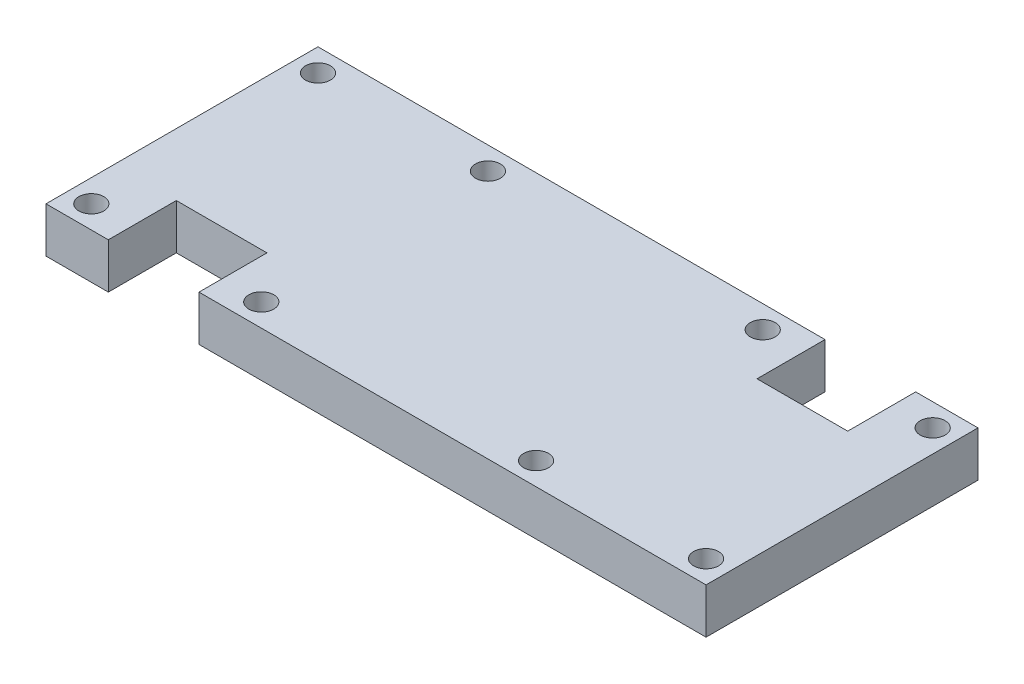
SolidWorks part; units mm, degrees
material "Alliage 1060"
ref_plane "Plan de face" through (0, 0, 0) normal (0, 0, 1) x (1, 0, 0)
ref_plane "Plan de dessus" through (0, 0, 0) normal (0, 1, 0) x (1, 0, 0)
ref_plane "Plan de droite" through (0, 0, 0) normal (1, 0, 0) x (0, 0, -1)
sketch "Esquisse1" plane through (0, 0, 0) normal (0, 1, 0) x (1, 0, 0)
  line L0 (0, 0) -> (38, 0)
  line L1 (38, 0) -> (38, 48) construction
  line L2 (38, 48) -> (0, 48)
  line L3 (0, 48) -> (0, 0)
  line L4 (58.25, 48) -> (58.25, 0) construction
  line L5 (116.5, 48) -> (116.5, 0)
  line L6 (78.5, 48) -> (116.5, 48)
  line L7 (78.5, 0) -> (78.5, 48) construction
  line L8 (116.5, 0) -> (78.5, 0)
  line L9 (38, 48) -> (78.5, 48)
  line L10 (38, 0) -> (78.5, 0)
  dimension "D1" = 38
  dimension "D2" = 48
  dimension "D3" = 20.25
extrude "Boss.-Extru.1" add sketch "Esquisse1" along normal blind 8
sketch "Esquisse3" plane through (0, 0, 0) normal (0, -1, 0) x (1, 0, 0)
  line L0 (0, 0) -> (8, 0) construction
  line L1 (0, 0) -> (116.5, 0) construction
  line L2 (8, 0) -> (8, -8) construction
  line L3 (8, -8) -> (0, 0) construction
  line L4 (0, 0) -> (8, 0) construction
  line L5 (8, 0) -> (0, -8) construction
  line L6 (0, -48) -> (0, 0) construction
  line L7 (0, -8) -> (0, -48) construction
  line L8 (116.5, -48) -> (0, -48) construction
  line L9 (0, -48) -> (8, -48) construction
  line L10 (8, -48) -> (8, -40) construction
  line L11 (8, -40) -> (0, -48) construction
  line L12 (0, -48) -> (8, -48) construction
  line L13 (8, -48) -> (0, -40) construction
  line L14 (38, 0) -> (38, -8) construction
  line L16 (38, -8) -> (30, -8) construction
  line L17 (30, -8) -> (30, 0) construction
  line L18 (30, -8) -> (38, 0) construction
  line L19 (38, 0) -> (30, 0) construction
  line L20 (30, 0) -> (38, -8) construction
  line L21 (38, -8) -> (38, -48) construction
  line L22 (38, -48) -> (30, -48) construction
  line L23 (30, -48) -> (30, -40) construction
  line L24 (30, -40) -> (38, -48) construction
  line L25 (38, -48) -> (30, -48) construction
  line L26 (30, -48) -> (38, -40) construction
  line L27 (38, -40) -> (30, -40) construction
  line L28 (58.25, 0) -> (58.25, -48) construction
  line L29 (0, 0) -> (116.5, 0) construction
  line L30 (116.5, -48) -> (0, -48) construction
  line L31 (78.5, -40) -> (86.5, -40) construction
  line L32 (86.5, -48) -> (78.5, -40) construction
  line L33 (78.5, -48) -> (86.5, -48) construction
  line L34 (86.5, -40) -> (78.5, -48) construction
  line L35 (86.5, -48) -> (86.5, -40) construction
  line L36 (78.5, -48) -> (86.5, -48) construction
  line L37 (78.5, -8) -> (78.5, -48) construction
  line L38 (86.5, 0) -> (78.5, -8) construction
  line L39 (78.5, 0) -> (86.5, 0) construction
  line L40 (86.5, -8) -> (78.5, 0) construction
  line L41 (86.5, -8) -> (86.5, 0) construction
  line L42 (78.5, -8) -> (86.5, -8) construction
  line L43 (78.5, 0) -> (78.5, -8) construction
  line L44 (108.5, -48) -> (116.5, -40) construction
  line L45 (116.5, -48) -> (108.5, -48) construction
  line L46 (108.5, -40) -> (116.5, -48) construction
  line L47 (108.5, -48) -> (108.5, -40) construction
  line L48 (116.5, -48) -> (108.5, -48) construction
  line L49 (116.5, -8) -> (116.5, -48) construction
  line L50 (108.5, 0) -> (116.5, -8) construction
  line L51 (116.5, 0) -> (108.5, 0) construction
  line L52 (108.5, -8) -> (116.5, 0) construction
  line L53 (108.5, 0) -> (108.5, -8) construction
  line L54 (116.5, 0) -> (108.5, 0) construction
  circle A0 centre (4, -4) radius 2.2
  circle A1 centre (34, -4) radius 2.2
  circle A2 centre (34, -44) radius 2.2
  circle A3 centre (4, -44) radius 2.2
  circle A4 centre (112.5, -44) radius 2.2
  circle A5 centre (82.5, -44) radius 2.2
  circle A6 centre (82.5, -4) radius 2.2
  circle A7 centre (112.5, -4) radius 2.2
  dimension "D1" = 4.4
  dimension "D2" = 4.4
  dimension "D6" = 4.4
  dimension "D9" = 4.4
  dimension "D3" = 8
  dimension "D4" = 11.3137
  dimension "D5" = 8
  dimension "D7" = 8
  dimension "D8" = 8
  dimension "D10" = 22
extrude "Enlèv. mat.-Extru.1" cut sketch "Esquisse3" against normal blind 8
sketch "Esquisse5" plane through (0, 8, 0) normal (0, 1, 0) x (1, 0, 0)
  line L1 (0, 48) -> (0, 0) construction
  line L2 (105.5, 48) -> (105.5, 36)
  line L8 (58.25, 48) -> (58.25, 0) construction
  line L9 (116.5, 48) -> (0, 48) construction
  line L10 (0, 0) -> (116.5, 0) construction
  line L17 (58.25, 24) -> (116.5, 24) construction
  line L18 (116.5, 0) -> (116.5, 48) construction
  line L29 (11, 0) -> (27, 0)
  line L30 (11, 0) -> (11, 12)
  line L31 (11, 12) -> (27, 12)
  line L32 (27, 0) -> (27, 12)
  line L33 (105.5, 48) -> (89.5, 48)
  line L34 (89.5, 48) -> (89.5, 36)
  line L35 (105.5, 36) -> (89.5, 36)
  point P20 (58.25, 24)
  point P28 (58.25, 24)
  dimension "D1" = 16
  dimension "D2" = 12
  dimension "D3" = 11
  dimension "D4" = 2
extrude "Enlèv. mat.-Extru.2" cut sketch "Esquisse5" against normal blind 8
